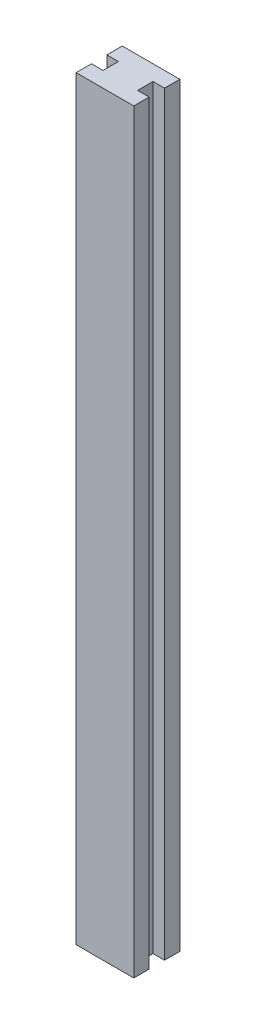
SolidWorks part; units mm, degrees
ref_plane "Front" through (0, 0, 0) normal (0, 0, 1) x (1, 0, 0)
ref_plane "Top" through (0, 0, 0) normal (0, 1, 0) x (1, 0, 0)
ref_plane "Right" through (0, 0, 0) normal (1, 0, 0) x (0, 0, -1)
sketch "Sketch1" plane through (0, 0, 0) normal (0, 1, 0) x (1, 0, 0)
  line L0 (0, 0) -> (5, 0)
  line L1 (5, 0) -> (5, 1.3333)
  line L2 (5, 1.3333) -> (4, 1.3333)
  line L3 (4, 1.3333) -> (4, 2.6667)
  line L4 (4, 2.6667) -> (5, 2.6667)
  line L5 (5, 2.6667) -> (5, 4)
  line L6 (5, 4) -> (0, 4)
  line L7 (0, 4) -> (0, 2.6667)
  line L8 (0, 2.6667) -> (1, 2.6667)
  line L9 (1, 2.6667) -> (1, 1.3333)
  line L10 (1, 1.3333) -> (0, 1.3333)
  line L11 (0, 1.3333) -> (0, 0)
  dimension "D1" = 5
  dimension "D2" = 4
  dimension "D3" = 1
  dimension "D4" = 1
extrude "Boss-Extrude1" add sketch "Sketch1" along normal blind 65.5
